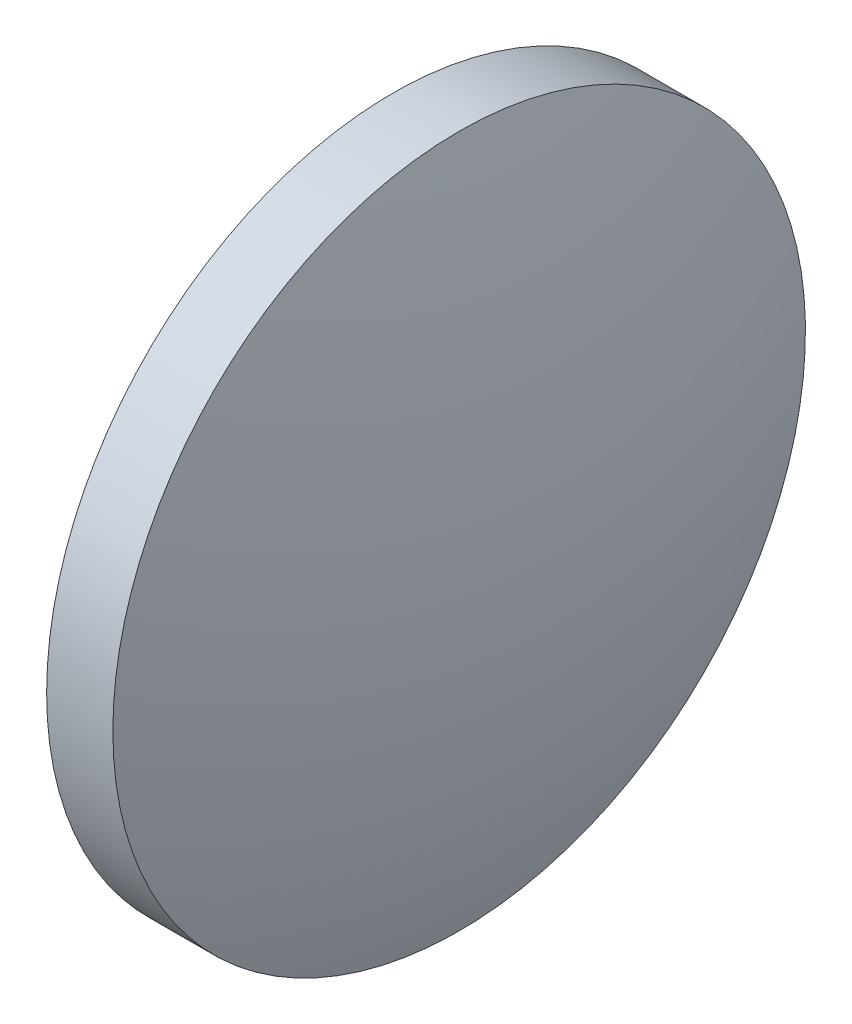
SolidWorks part; units mm, degrees
ref_plane "前视基准面" through (0, 0, 0) normal (0, 0, 1) x (1, 0, 0)
ref_plane "上视基准面" through (0, 0, 0) normal (0, 1, 0) x (1, 0, 0)
ref_plane "右视基准面" through (0, 0, 0) normal (1, 0, 0) x (0, 0, -1)
sketch "草图1" plane through (0, 0, 0) normal (0, 0, 1) x (1, 0, 0)
  line L0 (679.3383, 205.9902) -> (690.0949, 205.9902) construction
  line L1 (683.0636, 205.9902) -> (683.0636, 213.9902)
  line L2 (685.8636, 205.9902) -> (683.0636, 205.9902)
  line L5 (683.0636, 213.9902) -> (684.5936, 213.9902)
  arc A0 (685.8636, 205.9902) -> (684.5936, 213.9902) centre (660.0317, 205.9902) ccw
revolve "旋转1" add sketch "草图1" angle 360 about L0
